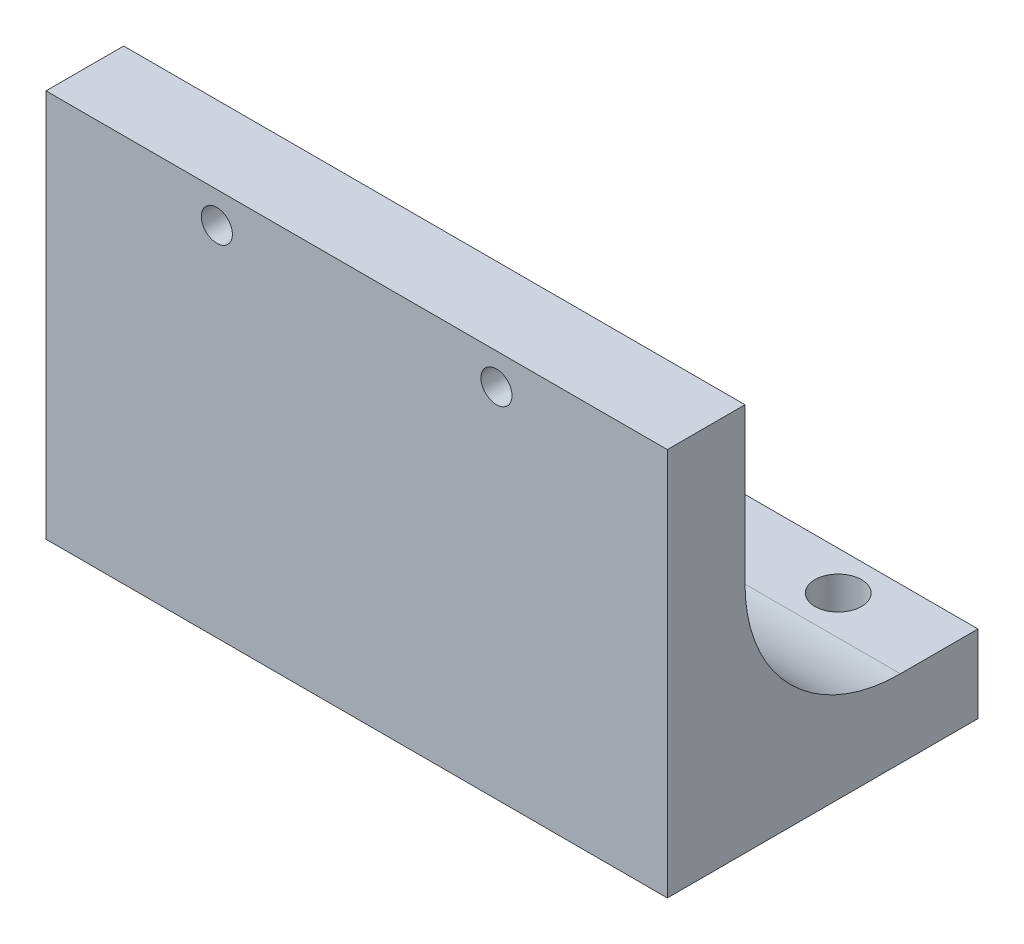
SolidWorks part; units mm, degrees
ref_plane "Front Plane" through (0, 0, 0) normal (0, 0, 1) x (1, 0, 0)
ref_plane "Top Plane" through (0, 0, 0) normal (0, 1, 0) x (1, 0, 0)
ref_plane "Right Plane" through (0, 0, 0) normal (1, 0, 0) x (0, 0, -1)
sketch "Sketch1" plane through (0, 0, 0) normal (0, 0, 1) x (1, 0, 0)
  line L0 (0, 12.5) -> (40, 12.5) construction
  line L1 (0, 0) -> (40, 0)
  line L2 (0, 0) -> (0, 25)
  line L3 (0, 25) -> (40, 25)
  line L4 (40, 0) -> (40, 25)
  circle A2 centre (11, 23) radius 1
  circle A3 centre (29, 23) radius 1
  point P12 (0, 0)
  dimension "D1" = 40
  dimension "D2" = 25
  dimension "D3" = 1
  dimension "D4" = 10
  dimension "D5" = 2
  dimension "D6" = 2
  dimension "D7" = 1
  dimension "D8" = 10
extrude "Boss-Extrude1" add sketch "Sketch1" along normal blind 5
sketch "Sketch2" plane through (0, 0, 0) normal (-1, 0, 0) x (0, 0, 1)
  line L1 (0, 0) -> (-15, 0)
  line L2 (0, 0) -> (0, 5)
  line L3 (0, 5) -> (-15, 5)
  line L4 (-15, 0) -> (-15, 5)
  dimension "D1" = 15
  dimension "D2" = 5
extrude "Boss-Extrude2" add sketch "Sketch2" against normal blind 40
fillet "Fillet2" radius 10 1 edges at (20, 5, 0)
sketch "Sketch8" plane through (0, 0, 0) normal (0, -1, 0) x (-1, 0, 0)
  line L0 (0, 7.0165) -> (-40, 7.0165) construction
  line L1 (0, 0) -> (0, 10) construction
  line L2 (-40, 10) -> (-40, 0) construction
  line L5 (0, 10) -> (0, 15) construction
  line L7 (-40, 15) -> (0, 15) construction
  line L10 (-40, 10) -> (-40, 15) construction
  circle A0 centre (-6.5, 12.5) radius 1.5
  circle A1 centre (-33.5, 12.5) radius 1.5
  dimension "D1" = 3
  dimension "D2" = 3
  dimension "D3" = 5
  dimension "D4" = 2.5
  dimension "D5" = 5
  dimension "D6" = 2.5
extrude "Cut-Extrude1" cut sketch "Sketch8" against normal blind 40
